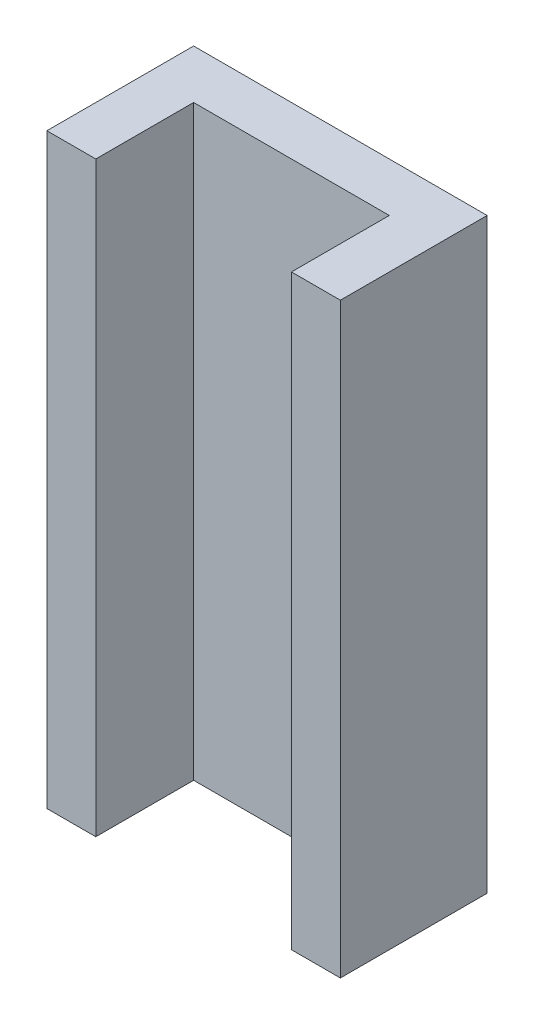
SolidWorks part; units mm, degrees
ref_plane "Front Plane" through (0, 0, 0) normal (0, 0, 1) x (1, 0, 0)
ref_plane "Top Plane" through (0, 0, 0) normal (0, 1, 0) x (1, 0, 0)
ref_plane "Right Plane" through (0, 0, 0) normal (1, 0, 0) x (0, 0, -1)
sketch "Sketch3" plane through (0, 0, 0) normal (0, 1, 0) x (1, 0, 0)
  line L0 (-19.05, 19.05) -> (19.05, 19.05)
  line L1 (-12.7, 12.7) -> (12.7, 12.7)
  line L2 (-12.7, 12.7) -> (-12.7, -12.7)
  line L3 (-12.7, -12.7) -> (12.7, -12.7)
  line L4 (12.7, 12.7) -> (12.7, -12.7)
  line L5 (-12.7, 12.7) -> (12.7, -12.7) construction
  line L6 (-12.7, -12.7) -> (12.7, 12.7) construction
  line L7 (19.05, 19.05) -> (19.05, -19.05)
  line L8 (-19.05, -19.05) -> (19.05, -19.05)
  line L9 (-19.05, 19.05) -> (-19.05, -19.05)
  line L10 (-19.05, 0) -> (19.05, 0)
  point P0 (0, 0)
  dimension "D1" = 25.4
  dimension "D2" = 6.35
extrude "Boss-Extrude1" add sketch "Sketch3" along normal mid plane 76.2 contours L9 L10 L2 L1 L4 L7 L0
